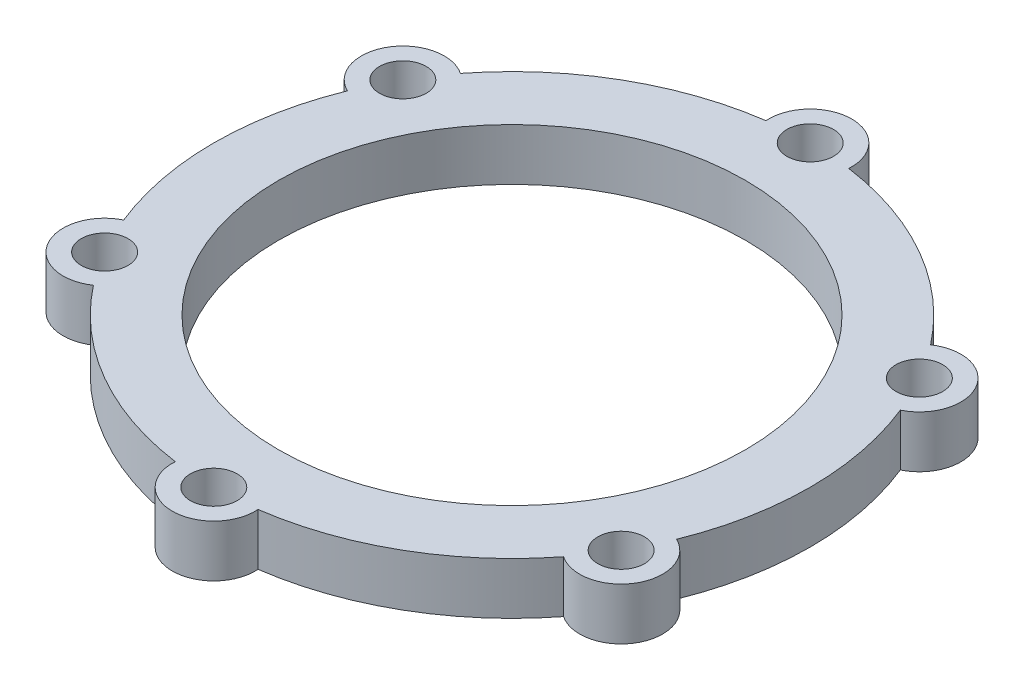
SolidWorks part; units mm, degrees
ref_plane "Front Plane" through (0, 0, 0) normal (0, 0, 1) x (1, 0, 0)
ref_plane "Top Plane" through (0, 0, 0) normal (0, 1, 0) x (1, 0, 0)
ref_plane "Right Plane" through (0, 0, 0) normal (1, 0, 0) x (0, 0, -1)
sketch "Sketch1" plane through (0, 0, 0) normal (0, 1, 0) x (1, 0, 0)
  line L0 (0, 0) -> (49.7965, 28.75) construction
  line L1 (49.7965, 28.75) -> (0, 0) construction
  line L2 (0, 0) -> (0, 57.5) construction
  circle A0 centre (0, 0) radius 45
  arc A1 (-7.9806, 56.9435) -> (-45.3242, 35.3832) centre (0, 0) ccw
  arc A2 (7.9806, 56.9435) -> (-7.9806, 56.9435) centre (0, 57.5) ccw
  circle A3 centre (0, 57.5) radius 4.5
  circle A4 centre (49.7965, 28.75) radius 4.5
  circle A5 centre (49.7965, -28.75) radius 4.5
  circle A6 centre (0, -57.5) radius 4.5
  circle A7 centre (-49.7965, -28.75) radius 4.5
  circle A8 centre (-49.7965, 28.75) radius 4.5
  arc A9 (53.3048, 21.5603) -> (45.3242, 35.3832) centre (49.7965, 28.75) ccw
  arc A10 (45.3242, -35.3832) -> (53.3048, -21.5603) centre (49.7965, -28.75) ccw
  arc A11 (-7.9806, -56.9435) -> (7.9806, -56.9435) centre (0, -57.5) ccw
  arc A12 (-53.3048, -21.5603) -> (-45.3242, -35.3832) centre (-49.7965, -28.75) ccw
  arc A13 (-45.3242, 35.3832) -> (-53.3048, 21.5603) centre (-49.7965, 28.75) ccw
  arc A14 (-53.3048, 21.5603) -> (-53.3048, -21.5603) centre (0, 0) ccw
  arc A15 (-45.3242, -35.3832) -> (-7.9806, -56.9435) centre (0, 0) ccw
  arc A16 (7.9806, -56.9435) -> (45.3242, -35.3832) centre (0, 0) ccw
  arc A17 (45.3242, 35.3832) -> (7.9806, 56.9435) centre (0, 0) ccw
  arc A18 (53.3048, -21.5603) -> (53.3048, 21.5603) centre (0, 0) ccw
  point P19 (0, 0)
  point P35 (0, 0)
  dimension "D1" = 90
  dimension "D2" = 115
  dimension "D3" = 9
  dimension "D4" = 16
  dimension "D7" = 60
  dimension "D5" = 6
  dimension "D6" = 6
extrude "Boss-Extrude1" add sketch "Sketch1" along normal blind 10
